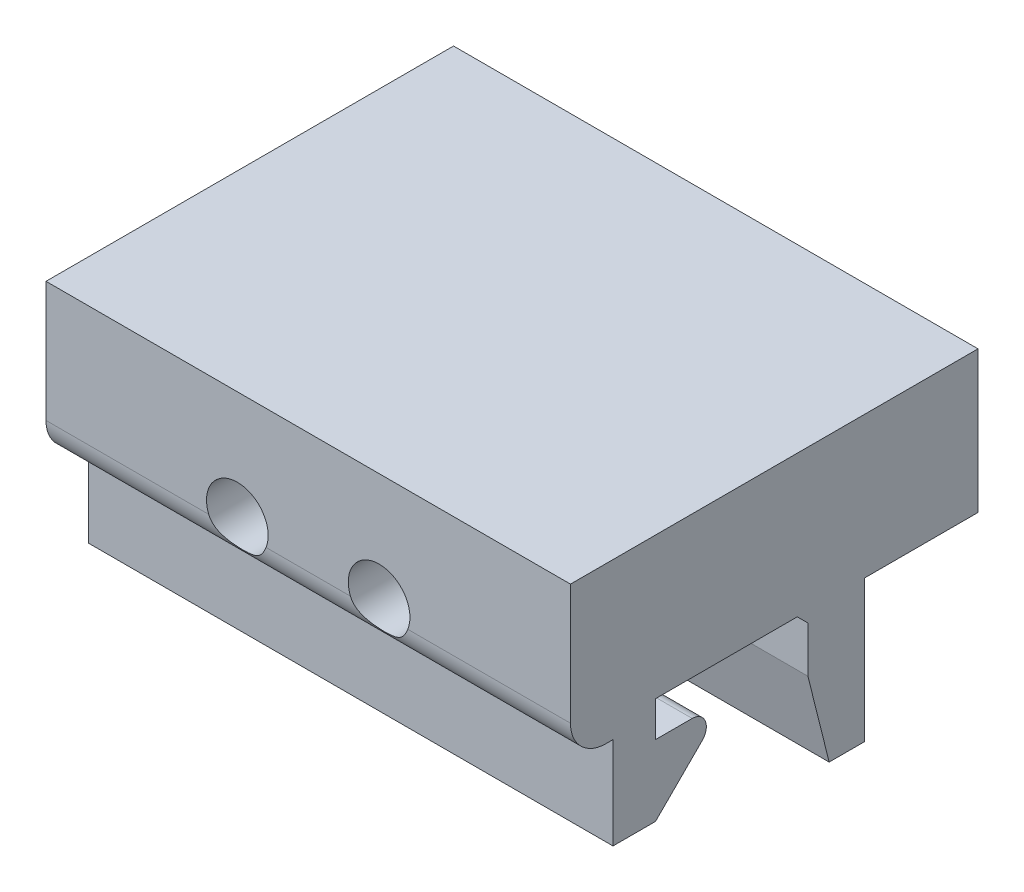
SolidWorks part; units mm, degrees
ref_plane "Front Plane" through (0, 0, 0) normal (0, 0, 1) x (1, 0, 0)
ref_plane "Top Plane" through (0, 0, 0) normal (0, 1, 0) x (1, 0, 0)
ref_plane "Right Plane" through (0, 0, 0) normal (1, 0, 0) x (0, 0, -1)
sketch "Sketch2" plane through (0, 0, 0) normal (1, 0, 0) x (0, 0, -1)
  line L0 (0, 0) -> (17.75, 0)
  line L1 (17.75, -10) -> (17.75, -20)
  line L2 (17.75, -20) -> (15.25, -20)
  line L3 (13.75, -14) -> (13.75, -10.75)
  line L4 (13.75, -10.75) -> (13, -10)
  line L5 (13, -10) -> (3, -10)
  line L6 (3, -10) -> (3, -12.5)
  line L7 (3, -12.5) -> (5.5858, -12.5)
  line L9 (3, -17.5) -> (0, -17.5)
  line L10 (0, -17.5) -> (0, -11)
  line L11 (6.2929, -14.2071) -> (3, -17.5)
  line L12 (0, 0) -> (-3, 0)
  line L13 (-3, 0) -> (-3, -8.5)
  line L14 (-0.5, -11) -> (0, -11)
  line L15 (15.25, -20) -> (13.75, -14)
  line L16 (17.75, 0) -> (25.75, 0)
  line L18 (17.75, -10) -> (25.75, -10)
  line L19 (25.75, 0) -> (25.75, -10)
  arc A0 (5.5858, -12.5) -> (6.2929, -14.2071) centre (5.5858, -13.5) cw
  arc A1 (-0.5, -11) -> (-3, -8.5) centre (-0.5, -8.5) cw
  point P16 (4.2929, -12.5)
  point P18 (8, -12.5)
  point P24 (-3, -11)
  dimension "D14" = 1
  dimension "D17" = 2.5
  dimension "D1" = 10.75
  dimension "D2" = 0.75
  dimension "D3" = 0.75
  dimension "D4" = 10
  dimension "D5" = 2.5
  dimension "D6" = 8
  dimension "D7" = 10
  dimension "D8" = 4
  dimension "D9" = 3
  dimension "D10" = 5
  dimension "D11" = 3
  dimension "D12" = 11
  dimension "D13" = 3
  dimension "D15" = 10
  dimension "D16" = 8
  dimension "D18" = 2.5
  dimension "D19" = 6
extrude "Boss-Extrude1" add sketch "Sketch2" along normal blind 37
sketch "Sketch3" plane through (0, 0, -17.75) normal (0, 0, -1) x (-1, 0, 0)
  line L3 (-37, 0) -> (0, 0) construction
  line L5 (-37, -10) -> (0, -10) construction
  circle A0 centre (-23.5, -7.7) radius 2.175
  circle A1 centre (-13.5, -7.7) radius 2.175
  point P9 (-18.5, 0)
  dimension "D1" = 4.35
  dimension "D2" = 4.35
  dimension "D3" = 5
  dimension "D4" = 5
  dimension "D5" = 2.3
  dimension "D6" = 2.3
extrude "Cut-Extrude1" cut sketch "Sketch3" against normal through all both and the other way through all contours A1 | A0
